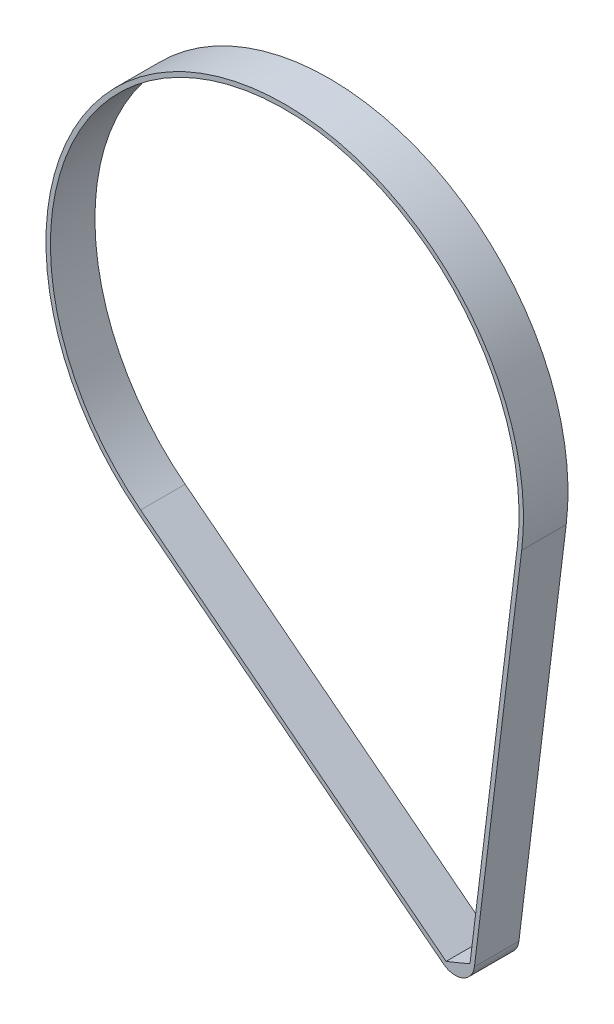
SolidWorks part; units mm, degrees
ref_plane "Front Plane" through (0, 0, 0) normal (0, 0, 1) x (1, 0, 0)
ref_plane "Top Plane" through (0, 0, 0) normal (0, 1, 0) x (1, 0, 0)
ref_plane "Right Plane" through (0, 0, 0) normal (1, 0, 0) x (0, 0, -1)
sketch "Sketch1" plane through (0, 0, 0) normal (0, 0, 1) x (1, 0, 0)
  line L0 (156.7087, -19.2777) -> (124.8399, -278.3394)
  line L1 (159.6863, -19.644) -> (127.8174, -278.7057)
  line L2 (-97.0799, -124.5181) -> (108.7661, -285.0048)
  line L3 (-98.9244, -126.884) -> (106.9216, -287.3707)
  arc A0 (156.7087, -19.2777) -> (-97.0799, -124.5181) centre (0, 0) ccw
  arc A1 (108.7661, -285.0048) -> (124.8399, -278.3394) centre (-47.3104, 114.0896) ccw
  arc A2 (106.9216, -287.3707) -> (127.8174, -278.7057) centre (114.9147, -277.1184) ccw
  arc A3 (159.6863, -19.644) -> (-98.9244, -126.884) centre (0, 0) ccw
  dimension "D1" = 3
extrude "Boss-Extrude1" add sketch "Sketch1" against normal blind 30
